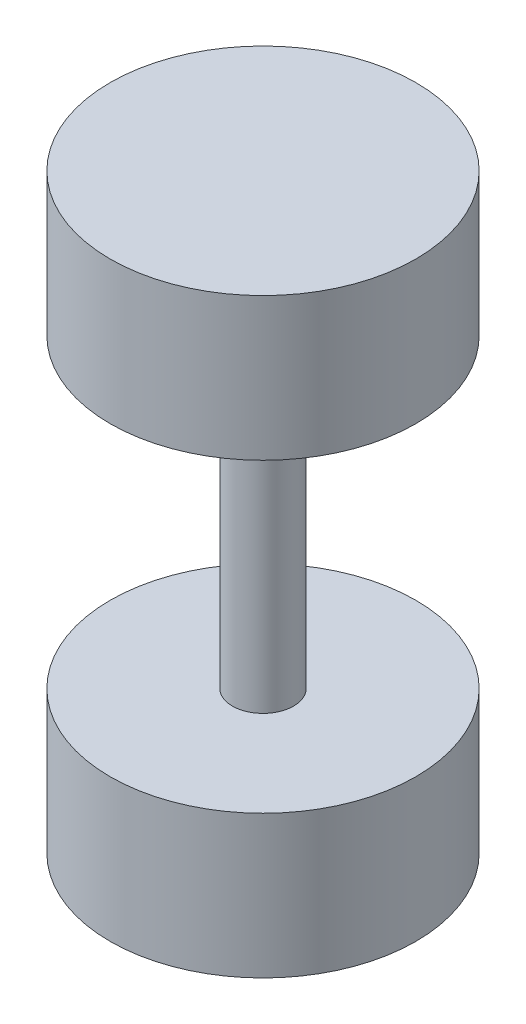
SolidWorks part; units mm, degrees
ref_plane "Front Plane" through (0, 0, 0) normal (0, 0, 1) x (1, 0, 0)
ref_plane "Top Plane" through (0, 0, 0) normal (0, 1, 0) x (1, 0, 0)
ref_plane "Right Plane" through (0, 0, 0) normal (1, 0, 0) x (0, 0, -1)
sketch "Sketch1" plane through (0, 0, 0) normal (0, 1, 0) x (1, 0, 0)
  circle A0 centre (0, 0) radius 7.5
  dimension "D1" = 15
extrude "Boss-Extrude1" add sketch "Sketch1" along normal blind 7
sketch "Sketch2" plane through (0, 7, 0) normal (0, 1, 0) x (1, 0, 0)
  circle A0 centre (0, 0) radius 1.5
  dimension "D1" = 3
extrude "Boss-Extrude2" add sketch "Sketch2" along normal blind 15
sketch "Sketch3" plane through (0, 0, 0) normal (0, -1, 0) x (1, 0, 0)
  line L1 (-2.5, -1.525) -> (2.5, -1.525)
  line L2 (-2.5, -1.525) -> (-2.5, 1.525)
  line L3 (-2.5, 1.525) -> (2.5, 1.525)
  line L4 (2.5, -1.525) -> (2.5, 1.525)
  line L5 (-2.5, -1.525) -> (2.5, 1.525) construction
  line L6 (-2.5, 1.525) -> (2.5, -1.525) construction
  point P1 (0, 0)
  dimension "D1" = 3.05
  dimension "D2" = 5
extrude "Cut-Extrude1" cut sketch "Sketch3" against normal blind 6
sketch "Sketch4" plane through (0, 22, 0) normal (0, 1, 0) x (1, 0, 0)
  circle A0 centre (0, 0) radius 7.5
  circle A1 centre (0, 0) radius 7.5 construction
extrude "Boss-Extrude3" add sketch "Sketch4" along normal blind 7
